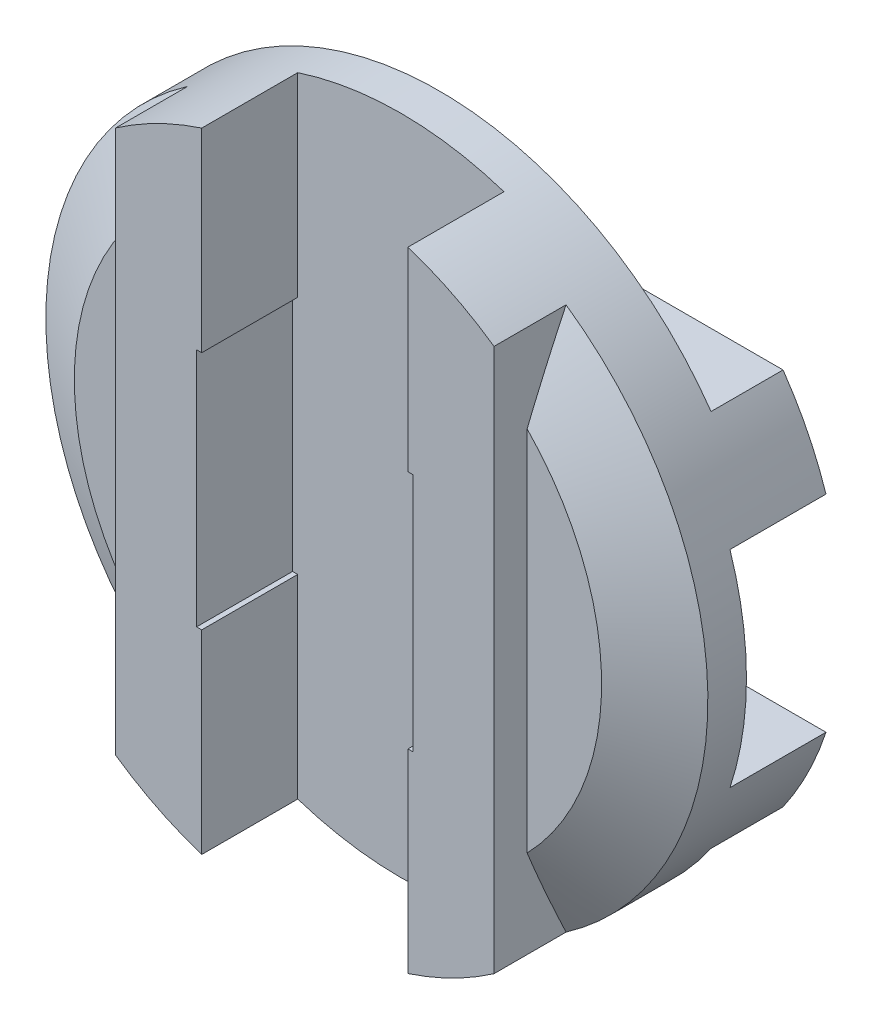
SolidWorks part; units mm, degrees
ref_plane "Front" through (0, 0, 0) normal (0, 0, 1) x (1, 0, 0)
ref_plane "Top" through (0, 0, 0) normal (0, 1, 0) x (1, 0, 0)
ref_plane "Right" through (0, 0, 0) normal (1, 0, 0) x (0, 0, -1)
sketch "Sketch1" plane through (0, 0, 0) normal (0, 0, 1) x (1, 0, 0)
  circle A0 centre (0, 0) radius 12.7
  point P3 (0, 12.7)
  dimension "OD" = 25.4
extrude "Boss-Extrude1" add sketch "Sketch1" against normal mid plane 7.9248
sketch "Sketch2" plane through (0, 0, 3.9624) normal (0, 0, 1) x (1, 0, 0)
  line L0 (-3.956, 12.7) -> (3.9561, -12.7) construction
  line L1 (-3.956, 12.7) -> (3.9561, 12.7)
  line L2 (-3.956, 12.7) -> (-3.956, -12.7)
  line L3 (-3.956, -12.7) -> (3.9561, -12.7)
  line L4 (3.9561, 12.7) -> (3.9561, -12.7)
  circle A0 centre (0, 0) radius 12.7 construction
  dimension "Tooth gap" = 7.9121
extrude "Cut-Extrude1" cut sketch "Sketch2" against normal blind 3.683
sketch "Sketch3" plane through (0, 0, -3.9624) normal (0, 0, -1) x (-1, 0, 0)
  line L1 (-12.7, 3.9561) -> (12.7, 3.9561)
  line L2 (-12.7, 3.9561) -> (-12.7, -3.956)
  line L3 (-12.7, -3.956) -> (12.7, -3.956)
  line L4 (12.7, 3.9561) -> (12.7, -3.956)
  line L14 (3.956, 12.7) -> (-3.9561, 12.7) construction
  line L15 (12.7, 3.9561) -> (-12.7, -3.956) construction
  circle A0 centre (0, 0) radius 12.7 construction
extrude "Cut-Extrude2" cut sketch "Sketch3" against normal blind 3.683
sketch "Sketch4" plane through (0, 0, 3.9624) normal (0, 0, 1) x (1, 0, 0)
  line L0 (-3.956, 0) -> (-7.2581, 0) construction
  line L1 (12.7, 12.7) -> (7.2581, 12.7)
  line L2 (12.7, 12.7) -> (12.7, -12.7)
  line L3 (12.7, -12.7) -> (7.2581, -12.7)
  line L4 (7.2581, 12.7) -> (7.2581, -12.7)
  line L5 (-12.7, 12.7) -> (-7.2581, 12.7)
  line L6 (-12.7, 12.7) -> (-12.7, -12.7)
  line L7 (-12.7, -12.7) -> (-7.258, -12.7)
  line L8 (-7.2581, 12.7) -> (-7.258, -12.7)
  line L9 (-3.956, 12.0681) -> (-3.956, -12.0681) construction
  line L10 (3.956, 0) -> (7.2581, 0) construction
  line L11 (3.9561, -12.0681) -> (3.9561, 12.0681) construction
  line L12 (-3.956, 12.7) -> (3.9561, 12.7) construction
  line L13 (-3.956, -12.7) -> (3.9561, -12.7) construction
  line L14 (3.9561, 12.7) -> (3.9561, -12.7) construction
  circle A1 centre (0, 0) radius 12.7 construction
  dimension "D1" = 5.4419
  dimension "Tooth thickness" = 3.302
extrude "Cut-Extrude3" cut sketch "Sketch4" against normal blind 1.27
sketch "Sketch5" plane through (0, 0, -3.9624) normal (0, 0, -1) x (-1, 0, 0)
  line L0 (-12.7, 12.7) -> (-7.2581, 12.7) construction
  line L1 (-12.7, 12.7) -> (12.7, 12.7)
  line L2 (-12.7, 12.7) -> (-12.7, 7.258)
  line L3 (-12.7, 7.258) -> (12.7, 7.258)
  line L4 (12.7, 12.7) -> (12.7, 7.258)
  line L5 (12.7, -12.7) -> (-12.7, -12.7)
  line L6 (12.7, -12.7) -> (12.7, -7.258)
  line L7 (12.7, -7.258) -> (-12.7, -7.258)
  line L8 (-12.7, -12.7) -> (-12.7, -7.258)
  line L9 (0, 3.9561) -> (0, 7.258) construction
  line L10 (-12.0681, 3.9561) -> (12.0681, 3.9561) construction
  line L11 (-12.7, 3.9561) -> (-12.7, -3.956) construction
  line L12 (0, -7.258) -> (0, -3.956) construction
  line L13 (-12.0681, -3.956) -> (12.0681, -3.956) construction
  circle A0 centre (0, 0) radius 12.7 construction
extrude "Cut-Extrude4" cut sketch "Sketch5" against normal blind 1.27
chamfer "Chamfer1" distance 2.5849 angle 30 4 edges at (0, -12.7, -2.6924) (0, 12.7, -2.6924) (-12.7, 0, 2.6924) (12.7, 0, 2.6924)
sketch "Sketch6" plane through (0, 0, 3.9624) normal (0, 0, 1) x (1, 0, 0)
  line L0 (-4.1539, 4.6037) -> (4.1539, -4.6037) construction
  line L1 (-4.1539, 4.6037) -> (4.1539, 4.6037)
  line L2 (-4.1539, 4.6037) -> (-4.1539, -4.6037)
  line L3 (-4.1539, -4.6037) -> (4.1539, -4.6037)
  line L4 (4.1539, 4.6037) -> (4.1539, -4.6037)
  dimension "D1" = 8.3077
  dimension "D2" = 9.2075
extrude "Cut-Extrude5" cut sketch "Sketch6" against normal up to surface (3.683 mm away) up to face at (0, 0, 0.2794)
sketch "Sketch7" plane through (0, 0, -3.9624) normal (0, 0, -1) x (-1, 0, 0)
  line L0 (-4.6037, 4.1539) -> (4.6037, -4.1539) construction
  line L1 (-4.6037, 4.1539) -> (4.6037, 4.1539)
  line L2 (-4.6037, 4.1539) -> (-4.6037, -4.1539)
  line L3 (-4.6037, -4.1539) -> (4.6037, -4.1539)
  line L4 (4.6037, 4.1539) -> (4.6037, -4.1539)
  line L5 (4.1539, 4.6037) -> (4.1539, -4.6037) construction
  line L6 (4.1539, 4.6037) -> (-4.1539, 4.6037) construction
extrude "Cut-Extrude6" cut sketch "Sketch7" against normal up to surface (3.683 mm away) up to face at (0, 0, -0.2794)
sketch "Sketch8" plane through (0, 0, 0) normal (1, 0, 0) x (0, 0, -1)
  line L0 (-3.9624, 12.0681) -> (-3.9624, 4.6037) construction
  line L2 (3.9624, 3.9561) -> (3.9624, 7.258) construction
  point P0 (3.9624, 12.7)
  point P1 (-3.9624, 12.7)
equation "\"D1@Cut-Extrude2\" = \"Tooth depth@Cut-Extrude1\""
equation "\"D1@Cut-Extrude4\" = \"Tooth depth 2@Cut-Extrude3\""
equation "\"D1@Chamfer1\" = \"D1@Sketch4\" * .475"
equation "\"D1@Sketch6\" = \"Tooth gap@Sketch2\" * 1.05"
equation "\"D2@Sketch6\" = \"OD@Sketch1\" * .3625"
